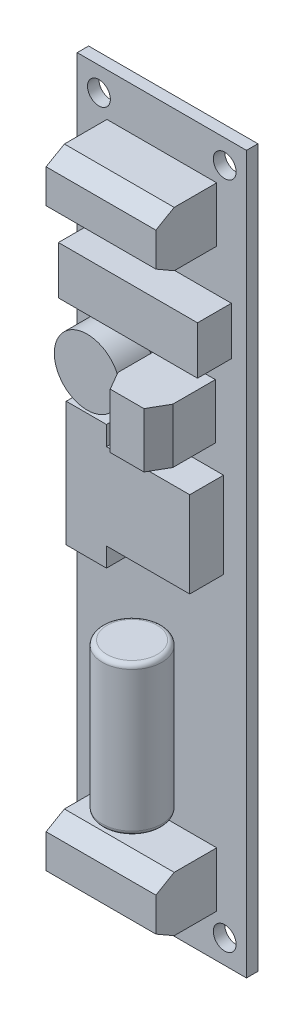
SolidWorks part; units mm, degrees
ref_plane "Front Plane" through (0, 0, 0) normal (0, 0, 1) x (1, 0, 0)
ref_plane "Top Plane" through (0, 0, 0) normal (0, 1, 0) x (1, 0, 0)
ref_plane "Right Plane" through (0, 0, 0) normal (1, 0, 0) x (0, 0, -1)
sketch "Sketch1" plane through (0, 0, 0) normal (0, 0, 1) x (1, 0, 0)
  line L1 (0, 0) -> (23.5, 0)
  line L2 (0, 0) -> (0, -99.5)
  line L3 (0, -99.5) -> (23.5, -99.5)
  line L4 (23.5, 0) -> (23.5, -99.5)
  dimension "D1" = 99.5
  dimension "D2" = 23.5
extrude "Boss-Extrude1" add sketch "Sketch1" along normal blind 1.5875
sketch "Sketch2" plane through (0, 0, 0) normal (0, 0, -1) x (-1, 0, 0)
  line L0 (-11.75, 0) -> (-11.75, -99.5) construction
  line L1 (-23.5, 0) -> (0, 0) construction
  line L2 (0, -99.5) -> (-23.5, -99.5) construction
  line L3 (-23.5, -49.75) -> (0, -49.75) construction
  line L4 (-23.5, -99.5) -> (-23.5, 0) construction
  line L5 (0, 0) -> (0, -99.5) construction
  circle A0 centre (-20.4813, -3.3156) radius 1.5875
  circle A1 centre (-3.0188, -3.3156) radius 1.5875
  circle A2 centre (-3.0188, -96.1844) radius 1.5875
  circle A3 centre (-20.4813, -96.1844) radius 1.5875
  dimension "D1" = 3.175
  dimension "D2" = 92.8688
  dimension "D3" = 17.4625
extrude "Cut-Extrude1" cut sketch "Sketch2" against normal through all
sketch "Sketch5" plane through (0, 0, 1.5875) normal (0, 0, 1) x (1, 0, 0)
  line L0 (11.75, 0) -> (11.75, -99.5) construction
  line L1 (4.13, -5.969) -> (19.37, -5.969)
  line L2 (4.13, -5.969) -> (4.13, -13.589)
  line L3 (4.13, -13.589) -> (19.37, -13.589)
  line L4 (19.37, -5.969) -> (19.37, -13.589)
  line L5 (11.562, -29.718) -> (19.182, -29.718)
  line L6 (11.562, -29.718) -> (11.562, -37.338)
  line L7 (11.562, -37.338) -> (19.182, -37.338)
  line L8 (19.182, -29.718) -> (19.182, -37.338)
  line L13 (23.5, 0) -> (0, 0) construction
  line L14 (0, -99.5) -> (23.5, -99.5) construction
  line L15 (0, 0) -> (0, -99.5) construction
  line L22 (0, -49.75) -> (23.5, -49.75) construction
  line L23 (23.5, -99.5) -> (23.5, 0) construction
  line L24 (19.37, -93.531) -> (19.37, -85.911)
  line L25 (4.13, -85.911) -> (19.37, -85.911)
  line L26 (4.13, -93.531) -> (4.13, -85.911)
  line L27 (4.13, -93.531) -> (19.37, -93.531)
  point P19 (11.75, -5.969)
  dimension "D1" = 15.24
  dimension "D2" = 7.62
  dimension "D3" = 5.969
  dimension "D4" = 7.62
  dimension "D5" = 7.62
  dimension "D6" = 4.318
  dimension "D7" = 29.718
extrude "Boss-Extrude2" add sketch "Sketch5" along normal blind 8.4455
chamfer "Chamfer1" distance 2.54 angle 30 6 edges at (11.75, -93.531, 10.033) (11.75, -85.911, 10.033) (19.182, -33.528, 10.033) (11.562, -33.528, 10.033) (11.75, -13.589, 10.033) (11.75, -5.969, 10.033)
ref_plane "Plane1" through (0, -83.371, 0) normal (0, 1, 0) x (1, 0, 0)
sketch "Sketch6" plane through (0, -83.371, 0) normal (0, 1, 0) x (1, 0, 0)
  line L0 (19.37, -1.5875) -> (4.13, -1.5875) construction
  line L1 (11.75, -1.5875) -> (11.75, -5.715) construction
  circle A0 centre (11.75, -5.715) radius 4.1275
  point P4 (11.75, -1.5875)
  point P6 (12.9515, -4.9039)
  point P7 (0, 0)
  point P8 (15.1043, -3.9026)
  dimension "D1" = 8.255
extrude "Boss-Extrude3" add sketch "Sketch6" along normal blind 20.701 separate body
fillet "Fillet1" radius 0.635 2 edges at (11.75, -83.371, 9.8425) (11.75, -62.67, 9.8425)
sketch "Sketch7" plane through (0, 0, 1.5875) normal (0, 0, 1) x (1, 0, 0)
  line L0 (11.75, 0) -> (11.75, -99.5) construction
  line L1 (23.5, 0) -> (0, 0) construction
  line L2 (0, -99.5) -> (23.5, -99.5) construction
  line L3 (0, 0) -> (0, -99.5) construction
  line L4 (2.098, -19.431) -> (21.402, -19.431)
  line L5 (2.098, -19.431) -> (2.098, -26.0985)
  line L6 (2.098, -26.0985) -> (21.402, -26.0985)
  line L7 (21.402, -19.431) -> (21.402, -26.0985)
  line L8 (8.7655, -52.578) -> (8.7655, -55.245)
  line L9 (8.7655, -40.64) -> (20.3225, -40.64)
  line L11 (8.7655, -52.578) -> (20.3225, -52.578)
  line L12 (20.3225, -40.64) -> (20.3225, -52.578)
  line L13 (3.1775, -37.973) -> (8.7655, -37.973)
  line L14 (3.1775, -37.973) -> (3.1775, -55.245)
  line L15 (3.1775, -55.245) -> (8.7655, -55.245)
  line L16 (8.7655, -37.973) -> (8.7655, -40.64)
  line L17 (3.1775, -46.609) -> (20.3225, -46.609) construction
  circle A0 centre (6.096, -33.02) radius 4.572
  point P4 (11.75, -19.431)
  point P23 (11.75, -46.609)
  dimension "D4" = 9.144
  dimension "D1" = 19.304
  dimension "D2" = 6.6675
  dimension "D3" = 19.431
  dimension "D5" = 6.096
  dimension "D6" = 17.145
  dimension "D7" = 33.02
  dimension "D8" = 17.272
  dimension "D9" = 11.938
  dimension "D10" = 5.588
  dimension "D11" = 40.64
extrude "Boss-Extrude4" add sketch "Sketch7" along normal blind 4.699
